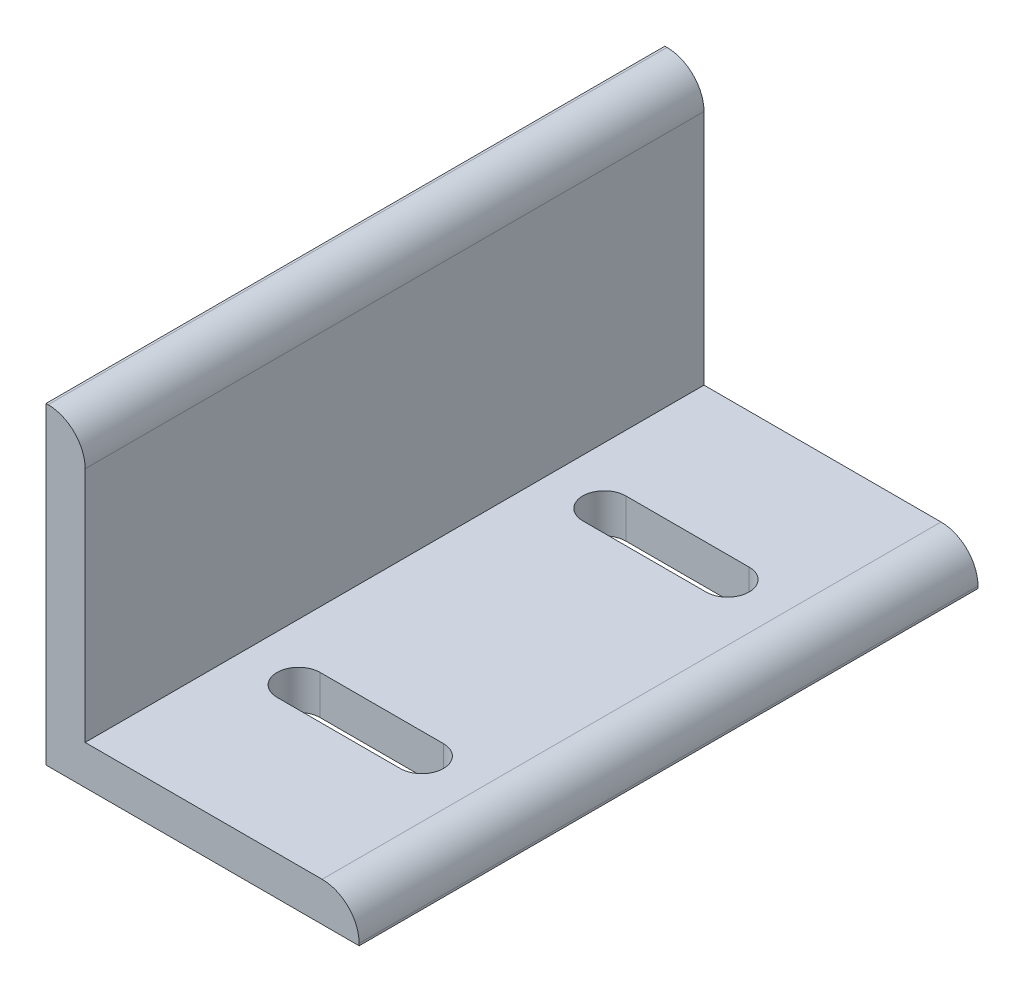
SolidWorks part; units mm, degrees
ref_plane "Front Plane" through (0, 0, 0) normal (0, 0, 1) x (1, 0, 0)
ref_plane "Top Plane" through (0, 0, 0) normal (0, 1, 0) x (1, 0, 0)
ref_plane "Right Plane" through (0, 0, 0) normal (1, 0, 0) x (0, 0, -1)
sketch "Sketch1" plane through (0, 0, 0) normal (0, 0, 1) x (1, 0, 0)
  line L0 (12.35, 6.35) -> (6.35, 6.35)
  line L1 (0, 0) -> (6.35, 0)
  line L2 (0, 0) -> (0, 50.8)
  line L3 (0, 50.8) -> (0.35, 50.8)
  line L4 (6.35, 6.35) -> (6.35, 44.8)
  line L5 (0, 0) -> (50.8, 0)
  line L6 (0, 0) -> (0, 6.35)
  line L7 (12.35, 6.35) -> (44.8, 6.35)
  line L8 (50.8, 0) -> (50.8, 0.35)
  arc A0 (44.8, 6.35) -> (50.8, 0.35) centre (44.8, 0.35) cw
  arc A1 (0.35, 50.8) -> (6.35, 44.8) centre (0.35, 44.8) cw
  point P10 (50.8, 6.35)
  point P13 (6.35, 50.8)
  dimension "D5" = 6
  dimension "D1" = 50.8
  dimension "D2" = 50.8
  dimension "D3" = 6.35
  dimension "D4" = 6.35
extrude "Boss-Extrude1" add sketch "Sketch1" along normal blind 100.4
ref_plane "Width Centerline Plane" through (0, 0, 50.2) normal (0, 0, 1) x (1, 0, 0)
sketch "Sketch2" plane through (0, 6.35, 0) normal (0, 1, 0) x (1, 0, 0)
  line L0 (25.575, -100.4) -> (25.575, 0) construction
  line L1 (6.35, -100.4) -> (44.8, -100.4) construction
  line L2 (6.35, 0) -> (44.8, 0) construction
  line L3 (15.575, -25.4) -> (35.575, -25.4) construction
  line L4 (15.575, -21.9) -> (35.575, -21.9)
  line L5 (15.575, -28.9) -> (35.575, -28.9)
  line L6 (50.8, -50.2) -> (0, -50.2) construction
  line L7 (50.8, -100.4) -> (50.8, 0) construction
  line L8 (0, -100.4) -> (0, 0) construction
  line L9 (15.575, -75) -> (35.575, -75) construction
  line L10 (15.575, -78.5) -> (35.575, -78.5)
  line L11 (15.575, -71.5) -> (35.575, -71.5)
  arc A0 (15.575, -21.9) -> (15.575, -28.9) centre (15.575, -25.4) ccw
  arc A1 (35.575, -28.9) -> (35.575, -21.9) centre (35.575, -25.4) ccw
  arc A2 (15.575, -78.5) -> (15.575, -71.5) centre (15.575, -75) cw
  arc A3 (35.575, -71.5) -> (35.575, -78.5) centre (35.575, -75) cw
  point P8 (25.575, -25.4)
  point P21 (25.575, -75)
  dimension "D2" = 3.5
  dimension "D1" = 20
  dimension "D3" = 25.4
extrude "Cut-Extrude1" cut sketch "Sketch2" against normal blind 10
